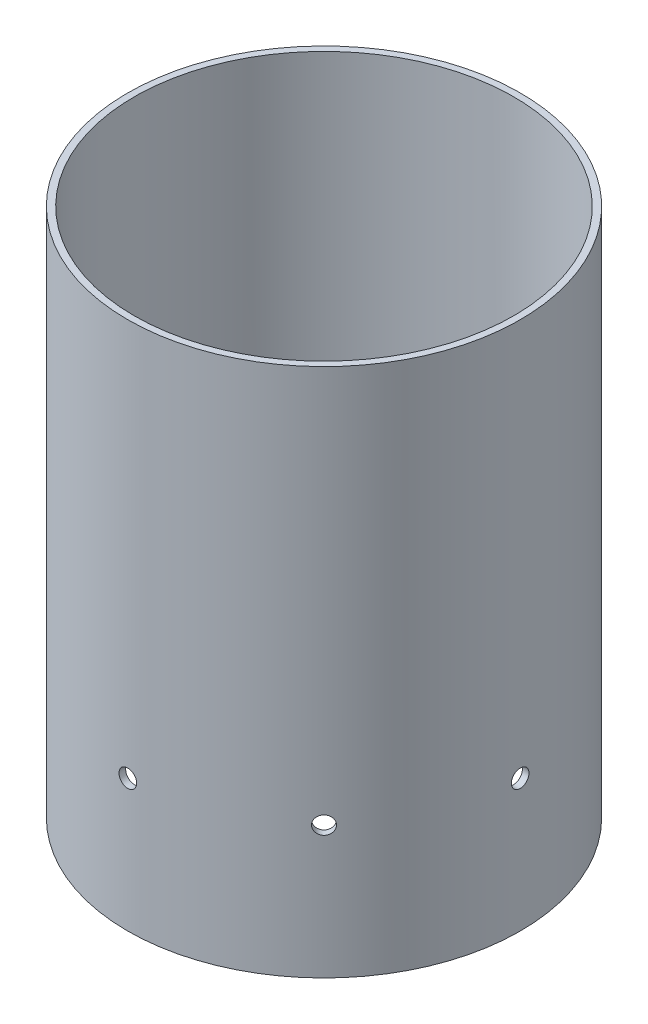
SolidWorks part; units mm, degrees
material "A-Glasfaser"
ref_plane "Ebene vorne" through (0, 0, 0) normal (0, 0, 1) x (1, 0, 0)
ref_plane "Ebene oben" through (0, 0, 0) normal (0, 1, 0) x (1, 0, 0)
ref_plane "Ebene rechts" through (0, 0, 0) normal (1, 0, 0) x (0, 0, -1)
sketch "Skizze1" plane through (0, 0, 0) normal (0, 1, 0) x (1, 0, 0)
  circle A0 centre (0, 0) radius 43
  circle A1 centre (0, 0) radius 44.5
  dimension "D1" = 89
  dimension "D2" = 86
extrude "Aufsatz-Linear austragen1" add sketch "Skizze1" along normal blind 120
sketch "Skizze2" plane through (0, 0, 0) normal (0, 0, 1) x (1, 0, 0)
  line L0 (0, 50) -> (0, 0) construction
  circle A0 centre (0, 50) radius 4
  dimension "D1" = 8
  dimension "D2" = 50
extrude "Schnitt-Linear austragen1" cut sketch "Skizze2" against normal through all
sketch "Skizze3" plane through (0, 0, 0) normal (0, 0, 1) x (1, 0, 0)
  line L0 (0, 0) -> (0, 30) construction
  circle A0 centre (0, 30) radius 2
  dimension "D2" = 4
  dimension "D1" = 30
extrude "Schnitt-Linear austragen2" cut sketch "Skizze3" against normal through all
pattern_circular "Kreismuster1" count 8 over 360 about axis through (0, 120, 0) along (0, -1, 0) of "Schnitt-Linear austragen2"
sketch "Skizze4" plane through (0, 0, 0) normal (0, 0, 1) x (1, 0, 0)
  line L3 (-44.5, 0) -> (44.5, 0) construction
  line L4 (-10, 0) -> (14, 0)
  line L5 (-10, 0) -> (-10, 24.319)
  line L6 (-10, 24.319) -> (14, 24.319)
  line L7 (14, 0) -> (14, 24.319)
  dimension "D2" = 14
  dimension "D1" = 24.319
  dimension "D3" = 10
extrude "Schnitt-Linear austragen3" cut sketch "Skizze4" against normal through all
fillet "Verrundung1" radius 2 2 edges at (-10, 24.319, -42.5914) (14, 24.319, -41.4487)
